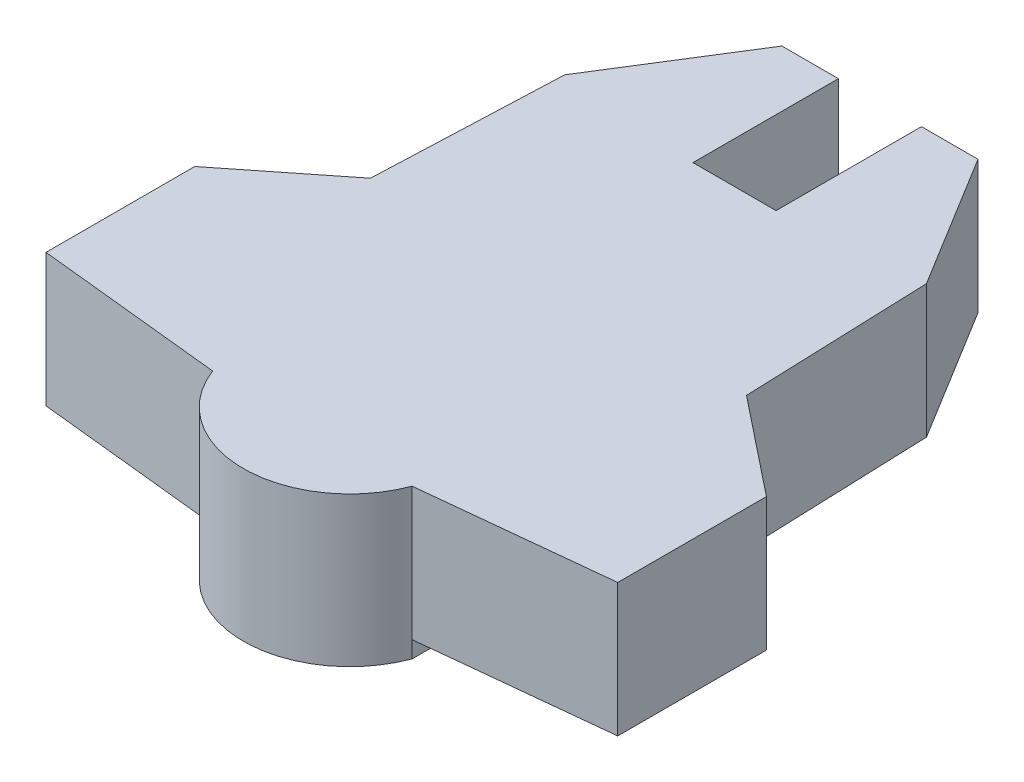
SolidWorks part; units mm, degrees
ref_plane "Front Plane" through (0, 0, 0) normal (0, 0, 1) x (1, 0, 0)
ref_plane "Top Plane" through (0, 0, 0) normal (0, 1, 0) x (1, 0, 0)
ref_plane "Right Plane" through (0, 0, 0) normal (1, 0, 0) x (0, 0, -1)
sketch "Sketch2" plane through (0, 0, 0) normal (0, 1, 0) x (1, 0, 0)
  line L0 (155.2798, 505.8339) -> (738.6131, 505.8339) construction
  line L3 (21.4236, 59.7566) -> (21.4236, 67.2801)
  line L4 (21.4236, 67.2801) -> (27.3205, 71.9569)
  line L5 (27.3205, 71.9569) -> (27.778, 83.1914)
  line L6 (27.778, 83.1914) -> (32.8106, 91.2233)
  line L7 (32.8106, 91.2233) -> (36.2106, 91.2233)
  line L8 (36.2106, 91.2233) -> (36.2106, 82.4733)
  line L9 (36.2106, 82.4733) -> (41.2106, 82.4733)
  line L10 (41.2106, 82.4733) -> (41.2106, 91.2233)
  line L11 (41.2106, 91.2233) -> (44.6106, 91.2233)
  line L12 (44.6106, 91.2233) -> (49.5416, 83.1914)
  line L13 (49.5416, 83.1914) -> (49.9483, 71.9569)
  line L14 (49.9483, 71.9569) -> (55.8236, 67.2801)
  line L15 (55.8236, 67.2801) -> (55.8236, 58.3332)
  line L16 (55.8236, 58.3332) -> (44.6236, 57.164)
  line L17 (21.4236, 59.7566) -> (21.4236, 58.3332)
  line L18 (21.4236, 58.3332) -> (32.6236, 57.164)
  arc A0 (32.6236, 57.164) -> (44.6236, 57.164) centre (38.6236, 59.4111) ccw
  dimension "D15" = 6.407
  dimension "D1" = 11.2345
  dimension "D2" = 21.4236
  dimension "D3" = 27.3205
  dimension "D4" = 8.9469
  dimension "D5" = 11.2
  dimension "D6" = 27.778
  dimension "D7" = 32.8106
  dimension "D8" = 3.4
  dimension "D9" = 5
  dimension "D10" = 12
  dimension "D11" = 57.164
  dimension "D12" = 4.6768
  dimension "D13" = 8.75
  dimension "D14" = 58.3332
  dimension "D16" = 59.7566
  dimension "D17" = 49.5416
  dimension "D18" = 49.9483
  dimension "D20" = 82.4733
extrude "Boss-Extrude1" add sketch "Sketch2" along normal blind 9
sketch "Sketch3" plane through (0, 0, 0) normal (0, -1, 0) x (1, 0, 0)
  line L0 (21.4236, -67.2801) -> (21.4236, -58.3332) construction
  circle A1 centre (38.6701, -68.7406) radius 2.5
  dimension "D1" = 5
  dimension "D2" = 17.2465
  dimension "D3" = 8.9469
  dimension "D4" = 1.4605
extrude "Boss-Extrude2" add sketch "Sketch3" along normal blind 6
sketch "Sketch4" plane through (0, 0, 0) normal (0, -1, 0) x (1, 0, 0)
  line L0 (32.6236, -57.164) -> (21.4236, -58.3332)
  line L1 (21.4236, -58.3332) -> (21.4236, -67.2801)
  line L2 (21.4236, -67.2801) -> (27.3205, -71.9569)
  line L3 (27.3205, -71.9569) -> (27.778, -83.1914)
  line L4 (27.778, -83.1914) -> (32.8106, -91.2233)
  line L5 (32.8106, -91.2233) -> (36.2106, -91.2233)
  line L6 (36.2106, -91.2233) -> (36.2106, -82.4733)
  line L7 (36.2106, -82.4733) -> (32.6236, -72.9675)
  line L8 (32.6236, -72.9675) -> (32.6236, -57.164)
  line L9 (44.6236, -57.164) -> (44.6236, -72.9675)
  line L10 (44.6236, -72.9675) -> (41.2106, -82.4733)
  line L11 (41.2106, -82.4733) -> (41.2106, -91.2233)
  line L12 (41.2106, -91.2233) -> (44.6106, -91.2233)
  line L13 (44.6106, -91.2233) -> (49.5416, -83.1914)
  line L14 (49.5416, -83.1914) -> (49.9483, -71.9569)
  line L15 (49.9483, -71.9569) -> (55.8236, -67.2801)
  line L16 (55.8236, -67.2801) -> (55.8236, -58.3332)
  line L17 (55.8236, -58.3332) -> (44.6236, -57.164)
  dimension "D1" = 14.6343
extrude "Cut-Extrude1" cut sketch "Sketch4" against normal blind 1
